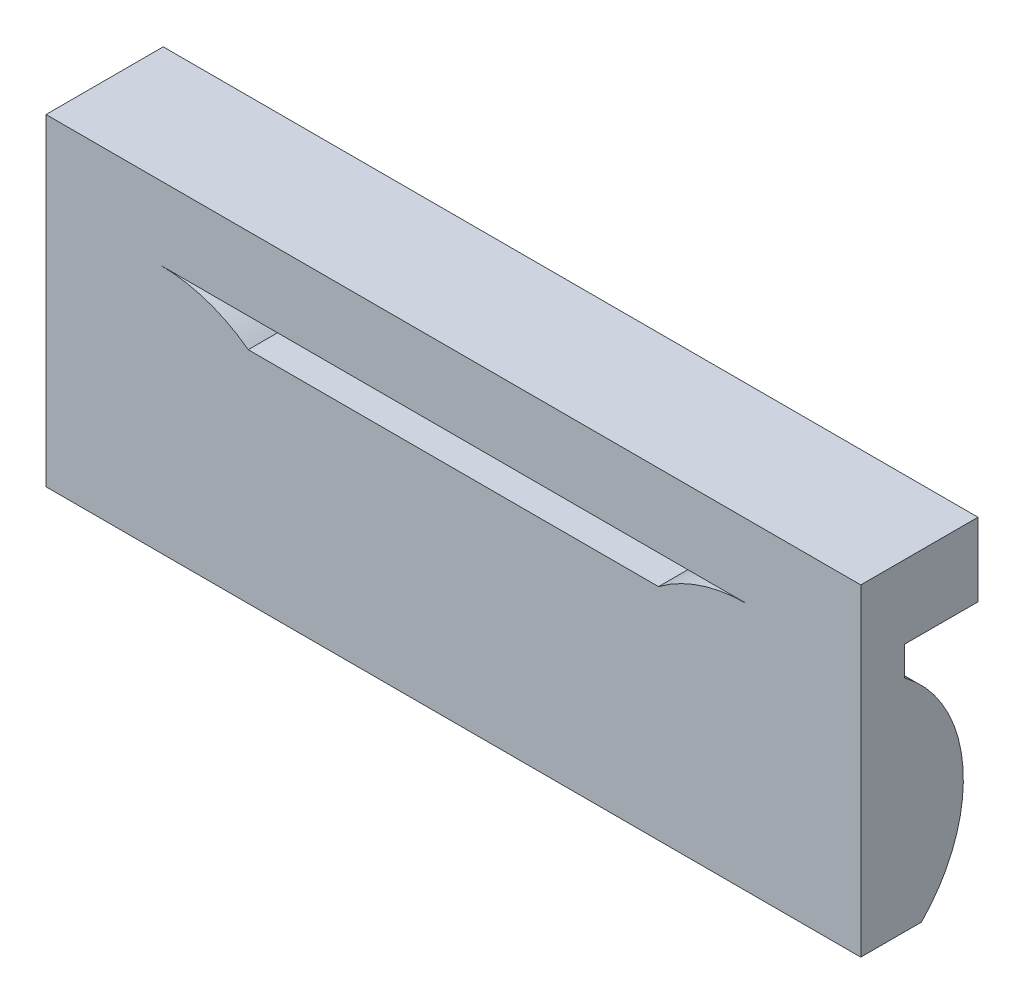
SolidWorks part; units mm, degrees
ref_plane "Front Plane" through (0, 0, 0) normal (0, 0, 1) x (1, 0, 0)
ref_plane "Top Plane" through (0, 0, 0) normal (0, 1, 0) x (1, 0, 0)
ref_plane "Right Plane" through (0, 0, 0) normal (1, 0, 0) x (0, 0, -1)
sketch "Sketch1" plane through (0, 0, 0) normal (0, 0, 1) x (1, 0, 0)
  line L0 (-6.95, 2.25) -> (-6.95, -2.25)
  line L1 (6.5, 2.25) -> (-6.5, 2.25)
  line L2 (6.5, 2.25) -> (6.5, -2.25)
  line L3 (6.5, -2.25) -> (-6.5, -2.25)
  line L4 (-6.5, 2.25) -> (-6.5, -2.25)
  line L5 (6.5, 2.25) -> (-6.5, -2.25) construction
  line L6 (6.5, -2.25) -> (-6.5, 2.25) construction
  line L7 (6.95, 2.25) -> (6.95, -2.25)
  line L8 (6.5, 2.75) -> (-6.5, 2.75)
  line L9 (6.5, -2.75) -> (-6.5, -2.75)
  line L10 (-6.95, 2.25) -> (-6.95, 2.75)
  line L11 (-6.95, 2.75) -> (-6.5, 2.75)
  line L12 (-6.95, -2.25) -> (-6.95, -2.75)
  line L13 (-6.95, -2.75) -> (-6.5, -2.75)
  line L14 (6.5, -2.75) -> (6.95, -2.75)
  line L15 (6.95, -2.75) -> (6.95, -2.25)
  line L16 (6.95, 2.25) -> (6.95, 2.75)
  line L17 (6.95, 2.75) -> (6.5, 2.75)
  line L18 (-5, 1.5) -> (5, 1.5)
  line L20 (-5.835, -2.0198) -> (-5.835, -2.25) construction
  line L21 (0, 2.25) -> (0, -2.25) construction
  line L23 (5.835, 1) -> (5.835, -2.25) construction
  line L24 (-6.5, 1.875) -> (-6.5, 1)
  line L30 (6.5, 1.875) -> (6.5, 1)
  arc A0 (-5, 1.5) -> (-2.8349, -2.25) centre (-5, -1) cw
  arc A1 (5, 1.5) -> (2.8349, -2.25) centre (5, -1) ccw
  point P0 (0, 0)
  point P21 (-4.0978, -2.25)
  point P26 (0, 0)
  dimension "D10" = 2.5
  dimension "D1" = 13
  dimension "D2" = 4.5
  dimension "D7" = 0.75
  dimension "D8" = 10
  dimension "D9" = 0.665
  dimension "D3" = 0.45
  dimension "D4" = 0.45
  dimension "D5" = 0.5
  dimension "D6" = 0.5
extrude "Boss-Extrude1" add sketch "Sketch1" along normal mid plane 0.75 contours L16 L17 L8 L11 L10 L0 L12 L13 L9 L14 L15 L7 L4 L1 L2 L3 | L18 A1 L3 L2 L1 L4 A0 | A1 L18 A0 L3
sketch "Sketch2" plane through (0, 0, -0.375) normal (0, 0, -1) x (-1, 0, 0)
  line L0 (-6.5, 1.875) -> (-6.5, 1) construction
  line L1 (6.5, 1.875) -> (6.5, 1) construction
  line L2 (5, 1.5) -> (-5, 1.5) construction
  line L3 (-6.5, 1.875) -> (-6.5, 1)
  line L4 (6.5, 2.25) -> (-6.5, 2.25)
  line L5 (6.5, -2.25) -> (6.5, 2.25)
  line L6 (-6.5, -2.25) -> (6.5, -2.25)
  line L7 (-6.5, 2.25) -> (-6.5, -2.25)
  line L8 (6.5, 2.25) -> (-6.5, 2.25)
  line L9 (6.5, -2.25) -> (6.5, 2.25)
  line L10 (-6.5, -2.25) -> (6.5, -2.25)
  line L11 (-6.5, 2.25) -> (-6.5, -2.25)
  line L12 (6.5, 1.875) -> (6.5, 1)
  line L13 (5, 1.5) -> (-5, 1.5)
  line L20 (-6.95, -2.25) -> (-6.95, -2.75)
  line L21 (-6.95, 2.25) -> (-6.95, -2.25)
  line L22 (-6.95, 2.75) -> (-6.95, 2.25)
  line L23 (-6.5, 2.75) -> (-6.95, 2.75)
  line L24 (6.5, 2.75) -> (-6.5, 2.75)
  line L25 (6.95, 2.75) -> (6.5, 2.75)
  line L26 (6.95, 2.25) -> (6.95, 2.75)
  line L27 (6.95, -2.25) -> (6.95, 2.25)
  line L28 (6.95, -2.75) -> (6.95, -2.25)
  line L29 (6.5, -2.75) -> (6.95, -2.75)
  line L30 (-6.5, -2.75) -> (6.5, -2.75)
  line L31 (-6.95, -2.75) -> (-6.5, -2.75)
  line L32 (-6.95, -2.25) -> (-6.95, -2.75)
  line L33 (-6.95, 2.25) -> (-6.95, -2.25)
  line L34 (-6.95, 2.75) -> (-6.95, 2.25)
  line L35 (-6.5, 2.75) -> (-6.95, 2.75)
  line L36 (6.5, 2.75) -> (-6.5, 2.75)
  line L37 (6.95, 2.75) -> (6.5, 2.75)
  line L38 (6.95, 2.25) -> (6.95, 2.75)
  line L39 (6.95, -2.25) -> (6.95, 2.25)
  line L40 (6.95, -2.75) -> (6.95, -2.25)
  line L41 (6.5, -2.75) -> (6.95, -2.75)
  line L42 (-6.5, -2.75) -> (6.5, -2.75)
  line L43 (-6.95, -2.75) -> (-6.5, -2.75)
  arc A0 (-2.8349, -2.25) -> (-5, 1.5) centre (-5, -1) ccw construction
  arc A1 (5, 1.5) -> (2.8349, -2.25) centre (5, -1) ccw construction
  arc A2 (-2.8349, -2.25) -> (-5, 1.5) centre (-5, -1) ccw
  arc A3 (5, 1.5) -> (2.8349, -2.25) centre (5, -1) ccw
  line M17 (-6.95, 2.75) -> (-6.95, -2.75)
  line M18 (-6.95, -2.75) -> (6.95, -2.75)
  line M19 (6.95, -2.75) -> (6.95, 2.75)
  line M20 (6.95, 2.75) -> (-6.95, 2.75)
  dimension "D1" = 0
  dimension "D2" = 0
extrude "Boss-Extrude2" add sketch "Sketch2" along normal blind 1.25 contours L11 L8 L9 L10 L3 M20 M17 M18 M19
sketch "Sketch3" plane through (0, 0, -0.375) normal (0, 0, -1) x (-1, 0, 0)
  line L0 (-6.5, 1.875) -> (-6.5, 1) construction
  line L1 (6.5, 1.875) -> (6.5, 1) construction
  line L2 (5, 1.5) -> (-5, 1.5) construction
  line L3 (-6.5, 1.875) -> (-6.5, 1)
  line L4 (6.5, 2.25) -> (-6.5, 2.25)
  line L5 (6.5, -2.25) -> (6.5, 2.25)
  line L6 (-6.5, -2.25) -> (6.5, -2.25)
  line L7 (-6.5, 2.25) -> (-6.5, -2.25)
  line L8 (6.5, 2.25) -> (-6.5, 2.25)
  line L9 (6.5, -2.25) -> (6.5, 2.25)
  line L10 (-6.5, -2.25) -> (6.5, -2.25)
  line L11 (-6.5, 2.25) -> (-6.5, -2.25)
  line L12 (6.5, 1.875) -> (6.5, 1)
  line L13 (5, 1.5) -> (-5, 1.5)
  line L20 (-6.95, -2.25) -> (-6.95, -2.75)
  line L21 (-6.95, 2.25) -> (-6.95, -2.25)
  line L22 (-6.95, 2.75) -> (-6.95, 2.25)
  line L23 (-6.5, 2.75) -> (-6.95, 2.75)
  line L24 (6.5, 2.75) -> (-6.5, 2.75)
  line L25 (6.95, 2.75) -> (6.5, 2.75)
  line L26 (6.95, 2.25) -> (6.95, 2.75)
  line L27 (6.95, -2.25) -> (6.95, 2.25)
  line L28 (6.95, -2.75) -> (6.95, -2.25)
  line L29 (6.5, -2.75) -> (6.95, -2.75)
  line L30 (-6.5, -2.75) -> (6.5, -2.75)
  line L31 (-6.95, -2.75) -> (-6.5, -2.75)
  line L32 (-6.95, -2.25) -> (-6.95, -2.75)
  line L33 (-6.95, 2.25) -> (-6.95, -2.25)
  line L34 (-6.95, 2.75) -> (-6.95, 2.25)
  line L35 (-6.5, 2.75) -> (-6.95, 2.75)
  line L36 (6.5, 2.75) -> (-6.5, 2.75)
  line L37 (6.95, 2.75) -> (6.5, 2.75)
  line L38 (6.95, 2.25) -> (6.95, 2.75)
  line L39 (6.95, -2.25) -> (6.95, 2.25)
  line L40 (6.95, -2.75) -> (6.95, -2.25)
  line L41 (6.5, -2.75) -> (6.95, -2.75)
  line L42 (-6.5, -2.75) -> (6.5, -2.75)
  line L43 (-6.95, -2.75) -> (-6.5, -2.75)
  arc A0 (-2.8349, -2.25) -> (-5, 1.5) centre (-5, -1) ccw construction
  arc A1 (5, 1.5) -> (2.8349, -2.25) centre (5, -1) ccw construction
  arc A2 (-2.8349, -2.25) -> (-5, 1.5) centre (-5, -1) ccw
  arc A3 (5, 1.5) -> (2.8349, -2.25) centre (5, -1) ccw
  dimension "D1" = 0
  dimension "D2" = 0
extrude "Boss-Extrude3" add sketch "Sketch3" along normal blind 2 contours A3 L13 A2 L10
sketch "Sketch4" plane through (0, 0, -2.375) normal (0, 0, -1) x (-1, 0, 0)
  line L0 (5, 1.5) -> (-5, 1.5) construction
  line L1 (3.5, -2.25) -> (-3.5, -2.25)
  line L2 (3.5, -2.25) -> (3.5, 2.25)
  line L3 (3.5, 2.25) -> (-3.5, 2.25)
  line L4 (-3.5, -2.25) -> (-3.5, 2.25)
  line L5 (3.5, -2.25) -> (-3.5, 2.25) construction
  line L6 (3.5, 2.25) -> (-3.5, -2.25) construction
  line L7 (-3.5, 1) -> (3.5, 1)
  line L8 (5, 1.5) -> (-5, 1.5)
  arc A0 (5, 1.5) -> (2.8349, -2.25) centre (5, -1) ccw construction
  arc A1 (-2.8349, -2.25) -> (-5, 1.5) centre (-5, -1) ccw construction
  arc A2 (5, 1.5) -> (2.8349, -2.25) centre (5, -1) ccw
  arc A3 (-2.8349, -2.25) -> (-5, 1.5) centre (-5, -1) ccw
  point P0 (0, 0)
  arc M5 (2.8349, -2.25) -> (5, 1.5) centre (5, -1) cw
  line M6 (5, 1.5) -> (-5, 1.5)
  arc M7 (-5, 1.5) -> (-2.8349, -2.25) centre (-5, -1) cw
  dimension "D1" = 4.5
  dimension "D2" = 7
  dimension "D3" = 0.75
extrude "Cut-Extrude1" cut sketch "Sketch4" against normal through all contours L4 L7 L2 M6 | L2 M5 M6 | L4 M7 M6
sketch "Sketch5" plane through (0, 0, 0) normal (1, 0, 0) x (0, 0, -1)
  line L0 (-1.125, 1.5) -> (3.875, 1.5)
  line L1 (-1.125, -3.5) -> (3.875, -3.5)
  line L2 (3.875, 1.5) -> (3.875, -3.5)
  line L4 (0.375, 1.5) -> (-0.375, 1.5)
  line L5 (-0.375, 1.5) -> (-0.375, 1)
  line L6 (-0.375, 1) -> (0.375, 1)
  line L7 (0.375, 1) -> (0.375, 1.5)
  line L8 (0.375, 1.5) -> (-0.375, 1.5)
  line L9 (-0.375, 1.5) -> (-0.375, 1)
  line L10 (-0.375, 1) -> (0.375, 1)
  line L11 (0.375, 1) -> (0.375, 1.5)
  arc A0 (-1.125, 1.5) -> (-1.125, -3.5) centre (-1.125, -1) cw
  dimension "D2" = 2.5
  dimension "D3" = 5
  dimension "D1" = 0
extrude "Cut-Extrude2" cut sketch "Sketch5" against normal through all both and the other way through all
